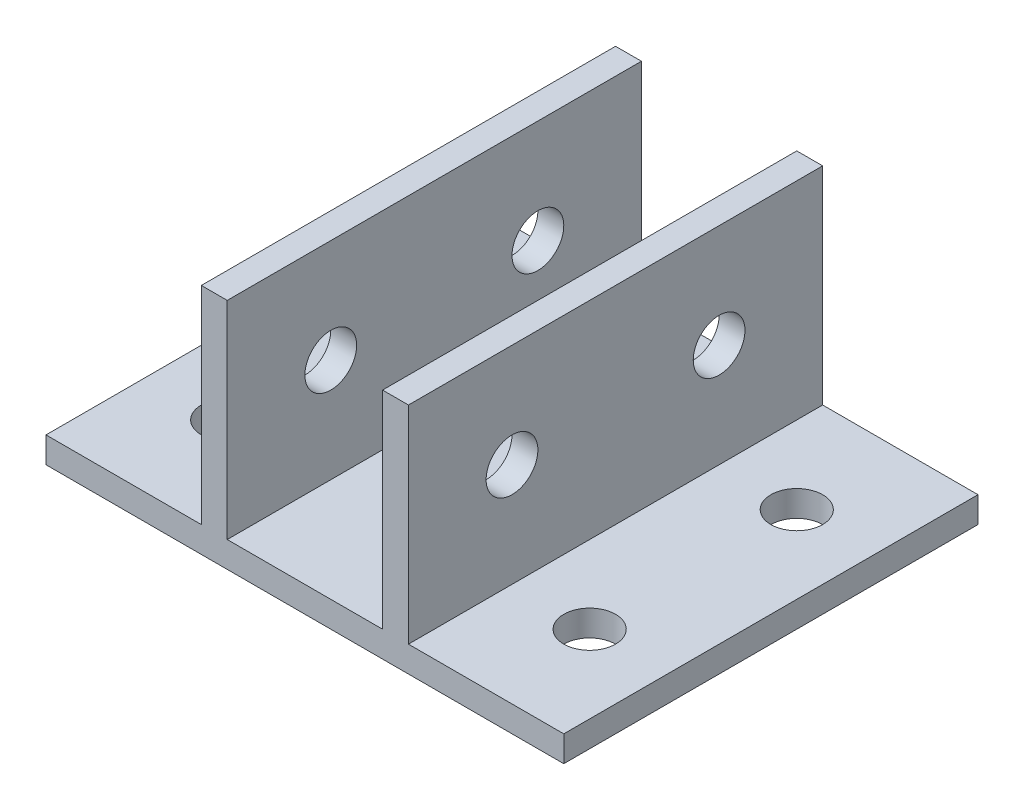
SolidWorks part; units mm, degrees
ref_plane "Front Plane" through (0, 0, 0) normal (0, 0, 1) x (1, 0, 0)
ref_plane "Top Plane" through (0, 0, 0) normal (0, 1, 0) x (1, 0, 0)
ref_plane "Right Plane" through (0, 0, 0) normal (1, 0, 0) x (0, 0, -1)
sketch "Sketch3" plane through (0, 0, 0) normal (0, 0, 1) x (1, 0, 0)
  line L0 (0, 0) -> (63.5, 0)
  line L1 (63.5, 0) -> (63.5, 3.175)
  line L2 (63.5, 3.175) -> (44.45, 3.175)
  line L3 (44.45, 3.175) -> (44.45, 28.575)
  line L4 (44.45, 28.575) -> (41.275, 28.575)
  line L5 (41.275, 28.575) -> (41.275, 3.175)
  line L6 (41.275, 3.175) -> (22.225, 3.175)
  line L7 (22.225, 3.175) -> (22.225, 28.575)
  line L8 (22.225, 28.575) -> (19.05, 28.575)
  line L9 (19.05, 28.575) -> (19.05, 3.175)
  line L10 (19.05, 3.175) -> (0, 3.175)
  line L11 (0, 3.175) -> (0, 0)
  dimension "D1" = 3.175
  dimension "D2" = 3.175
  dimension "D3" = 25.4
  dimension "D4" = 19.05
  dimension "D5" = 19.05
extrude "Boss-Extrude2" add sketch "Sketch3" along normal blind 50.8
sketch "Sketch4" plane through (19.05, 0, 0) normal (-1, 0, 0) x (0, 0, 1)
  line L0 (25.4, 28.575) -> (25.4, 3.175) construction
  line L1 (25.4, 15.875) -> (0, 15.875) construction
  line L2 (25.4, 15.875) -> (50.8, 15.875) construction
  line L4 (0, 28.575) -> (0, 3.175)
  line L5 (0, 3.175) -> (50.8, 3.175)
  line L6 (50.8, 3.175) -> (50.8, 28.575)
  line L7 (50.8, 28.575) -> (0, 28.575)
  line L8 (0, 28.575) -> (0, 3.175)
  line L9 (0, 3.175) -> (50.8, 3.175)
  line L10 (50.8, 3.175) -> (50.8, 28.575)
  line L11 (50.8, 28.575) -> (0, 28.575)
  circle A0 centre (12.7, 15.875) radius 3.175
  circle A1 centre (38.1, 15.875) radius 3.175
  point P9 (25.4, 15.875)
  dimension "D2" = 6.35
  dimension "D1" = 0
extrude "Cut-Extrude1" cut sketch "Sketch4" against normal through all contours A0 | A1
sketch "Sketch5" plane through (0, 3.175, 0) normal (0, 1, 0) x (1, 0, 0)
  line L0 (63.5, 0) -> (44.45, 0) construction
  line L1 (44.45, 0) -> (44.45, -50.8) construction
  line L2 (44.45, -50.8) -> (63.5, -50.8) construction
  line L3 (63.5, -50.8) -> (63.5, 0) construction
  line L4 (44.45, 0) -> (41.275, 0) construction
  line L5 (41.275, 0) -> (41.275, -50.8) construction
  line L6 (41.275, -50.8) -> (44.45, -50.8) construction
  line L7 (44.45, -50.8) -> (44.45, 0) construction
  line L8 (41.275, 0) -> (22.225, 0) construction
  line L9 (22.225, 0) -> (22.225, -50.8) construction
  line L10 (22.225, -50.8) -> (41.275, -50.8) construction
  line L11 (41.275, -50.8) -> (41.275, 0) construction
  line L12 (22.225, 0) -> (19.05, 0) construction
  line L13 (19.05, 0) -> (19.05, -50.8) construction
  line L14 (19.05, -50.8) -> (22.225, -50.8) construction
  line L15 (22.225, -50.8) -> (22.225, 0) construction
  line L16 (19.05, 0) -> (0, 0) construction
  line L17 (0, 0) -> (0, -50.8) construction
  line L18 (0, -50.8) -> (19.05, -50.8) construction
  line L19 (19.05, -50.8) -> (19.05, 0) construction
  line L20 (63.5, 0) -> (44.45, 0)
  line L21 (44.45, 0) -> (44.45, -50.8)
  line L22 (44.45, -50.8) -> (63.5, -50.8)
  line L23 (63.5, -50.8) -> (63.5, 0)
  line L24 (44.45, 0) -> (41.275, 0)
  line L25 (41.275, 0) -> (41.275, -50.8)
  line L26 (41.275, -50.8) -> (44.45, -50.8)
  line L27 (44.45, -50.8) -> (44.45, 0)
  line L28 (41.275, 0) -> (22.225, 0)
  line L29 (22.225, 0) -> (22.225, -50.8)
  line L30 (22.225, -50.8) -> (41.275, -50.8)
  line L31 (41.275, -50.8) -> (41.275, 0)
  line L32 (22.225, 0) -> (19.05, 0)
  line L33 (19.05, 0) -> (19.05, -50.8)
  line L34 (19.05, -50.8) -> (22.225, -50.8)
  line L35 (22.225, -50.8) -> (22.225, 0)
  line L36 (19.05, 0) -> (0, 0)
  line L37 (0, 0) -> (0, -50.8)
  line L38 (0, -50.8) -> (19.05, -50.8)
  line L39 (19.05, -50.8) -> (19.05, 0)
  line L40 (9.525, 0) -> (9.525, -12.7) construction
  line L41 (53.975, 0) -> (53.975, -12.7) construction
  line L42 (0, -25.4) -> (63.5, -25.4) construction
  line L43 (9.525, -50.8) -> (9.525, -38.1) construction
  line L44 (9.525, -12.7) -> (9.525, -25.4) construction
  line L45 (9.525, -25.4) -> (9.525, -38.1) construction
  line L46 (9.525, -38.1) -> (9.525, -50.8) construction
  line L47 (9.525, -12.7) -> (9.525, 0) construction
  line L48 (53.975, -50.8) -> (53.975, -38.1) construction
  line L49 (53.975, -12.7) -> (53.975, -25.4) construction
  line L50 (53.975, -25.4) -> (53.975, -38.1) construction
  line L51 (31.75, 0) -> (31.75, -50.8) construction
  circle A0 centre (9.525, -12.7) radius 3.175
  circle A1 centre (9.525, -38.1) radius 3.175
  circle A2 centre (53.975, -12.7) radius 3.175
  circle A3 centre (53.975, -38.1) radius 3.175
  point P26 (9.525, -25.4)
  point P31 (9.525, -25.4)
  point P34 (9.525, -25.4)
  point P36 (9.525, -25.4)
  point P39 (9.525, -25.4)
  dimension "D1" = 6.35
  dimension "D2" = 12.7
extrude "Cut-Extrude2" cut sketch "Sketch5" against normal through all contours A1 | A0 | A2 | A3
